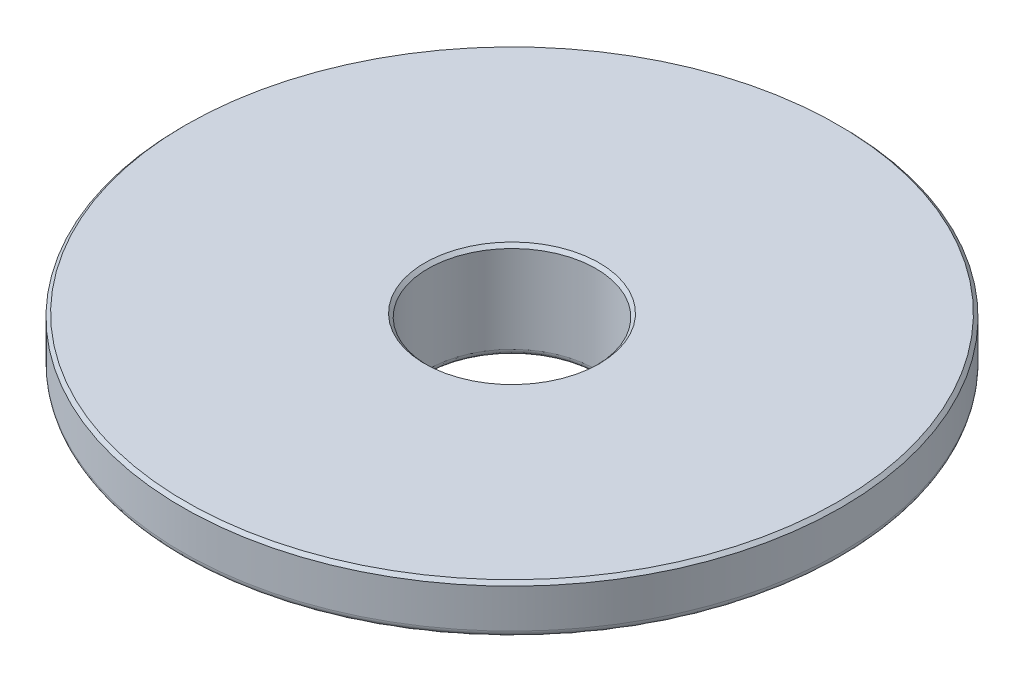
SolidWorks part; units mm, degrees
material "304 SSTL"
ref_plane "Front" through (0, 0, 0) normal (0, 0, 1) x (1, 0, 0)
ref_plane "Top" through (0, 0, 0) normal (0, 1, 0) x (1, 0, 0)
ref_plane "Right" through (0, 0, 0) normal (1, 0, 0) x (0, 0, -1)
sketch "Sketch1" plane through (0, 0, 0) normal (0, 0, 1) x (1, 0, 0)
  line L0 (0, 0) -> (0, -73.66) construction
  line L2 (7.62, -76.962) -> (25.4, -76.962)
  line L3 (25.4, -76.962) -> (25.4, -69.1421)
  line L6 (7.62, -73.2648) -> (7.62, -76.962)
  arc A0 (7.62, -73.2648) -> (25.4, -69.1421) centre (0, 0) ccw construction
  arc A1 (7.62, -73.2648) -> (25.4, -69.1421) centre (0, 0) ccw
  circle A2 centre (0, 0) radius 73.66 construction
  dimension "D1" = 147.32
  dimension "D2" = 7.62
  dimension "D3" = 25.4
  dimension "D4" = 3.302
sketch "Sketch2" plane through (0, 0, 0) normal (0, 0, 1) x (1, 0, 0)
  line L1 (0, 0) -> (0, -73.6727) construction
  line L2 (25.4, -65.5447) -> (25.4, -69.1557)
  line L3 (6.477, -73.3874) -> (6.477, -65.5447)
  line L4 (6.477, -65.5447) -> (25.4, -65.5447)
  line L5 (0, -73.6727) -> (0, -87.1962) construction
  arc A1 (6.477, -73.3874) -> (25.4, -69.1557) centre (0, 0) ccw
  circle A2 centre (0, 0) radius 73.6727 construction
  point P9 (0, -73.6727)
  dimension "D2" = 147.3454
  dimension "D1" = 8.128
  dimension "D3" = 6.477
  dimension "D4" = 18.923
revolve "Revolve2" add sketch "Sketch2" angle 360 about L5
sketch "Sketch3" plane through (0, 0, 0) normal (0, 0, 1) x (1, 0, 0)
  line L0 (6.477, -73.3874) -> (6.477, -73.1361)
  line L1 (6.477, -73.3874) -> (-6.477, -73.3874) construction
  line L2 (18.9841, -71.1848) -> (18.9841, -70.9308)
  line L3 (0, 0) -> (0, -59.4326) construction
  line L4 (18.9841, -70.9308) -> (6.477, -73.1361)
  arc A0 (6.477, -73.3874) -> (18.9841, -71.1848) centre (0, 0) ccw
  dimension "D1" = 147.3454
  dimension "D3" = 0.254
  dimension "D2" = 190
  dimension "D5" = 12.7
revolve "Cut-Revolve1" cut sketch "Sketch3" angle 360 about L3
chamfer "Chamfer2" distance 0.254 angle 45 2 edges at (-6.477, -65.5447, 0) (-25.4, -65.5447, 0)
fillet "Fillet2" radius 0.508 2 edges at (0, -73.1361, 6.477) (-25.4, -69.1557, 0)
fillet "Fillet3" radius 0.127 1 edges at (0, -71.1848, 18.9841)
